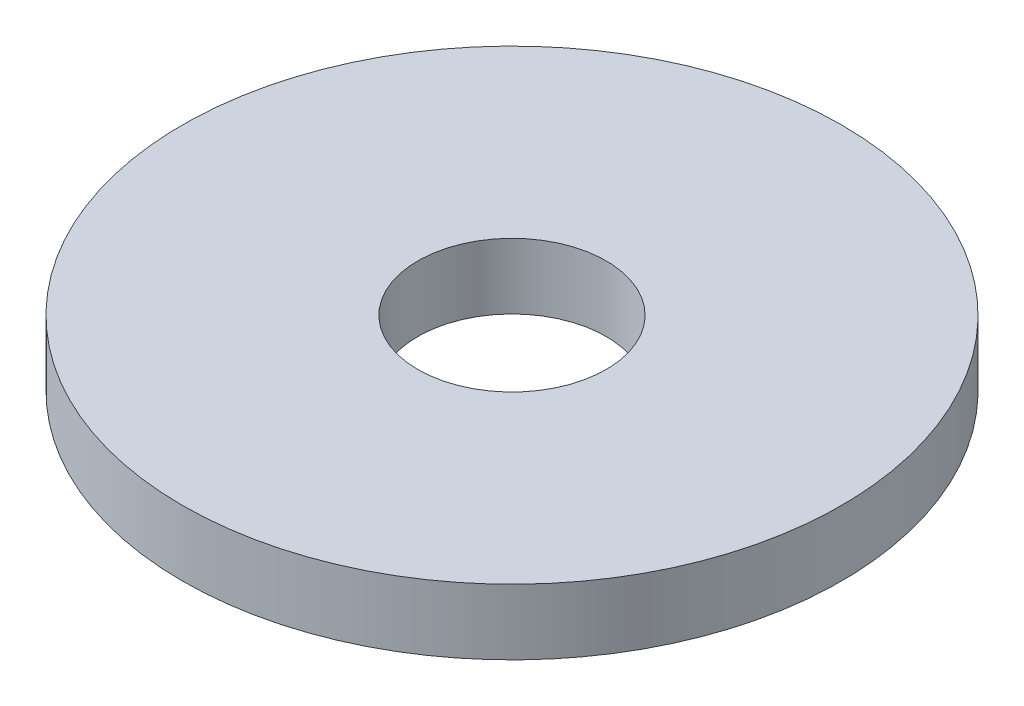
SolidWorks part; units mm, degrees
material "Delrin 2700 NC010, Low Viscosity Acetal Copolymer (SS)"
ref_plane "Front Plane" through (0, 0, 0) normal (0, 0, 1) x (1, 0, 0)
ref_plane "Top Plane" through (0, 0, 0) normal (0, 1, 0) x (1, 0, 0)
ref_plane "Right Plane" through (0, 0, 0) normal (1, 0, 0) x (0, 0, -1)
sketch "Sketch1" plane through (0, 0, 0) normal (0, 1, 0) x (1, 0, 0)
  circle A0 centre (0, 0) radius 11.1125
  circle A1 centre (0, 0) radius 3.175
  dimension "D1" = 22.225
  dimension "D2" = 6.35
extrude "Boss-Extrude1" add sketch "Sketch1" along normal blind 2.2098
